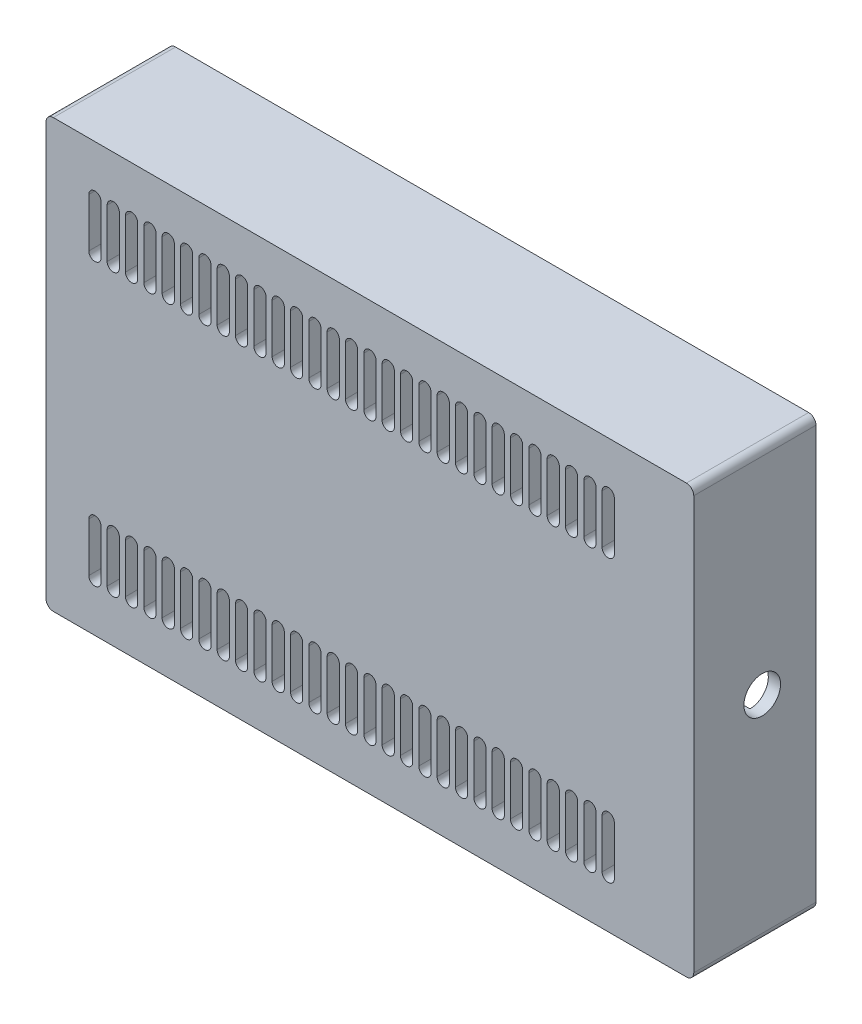
SolidWorks part; units mm, degrees
material "ABS"
ref_plane "Front Plane" through (0, 0, 0) normal (0, 0, 1) x (1, 0, 0)
ref_plane "Top Plane" through (0, 0, 0) normal (0, 1, 0) x (1, 0, 0)
ref_plane "Right Plane" through (0, 0, 0) normal (1, 0, 0) x (0, 0, -1)
sketch "Sketch1" plane through (0, 0, 0) normal (0, 0, 1) x (1, 0, 0)
  line L1 (-119.99, -87.5) -> (145.01, -87.5)
  line L2 (-119.99, -87.5) -> (-119.99, 87.5)
  line L3 (-119.99, 87.5) -> (145.01, 87.5)
  line L4 (145.01, -87.5) -> (145.01, 87.5)
  point P0 (-119.99, 0)
  dimension "D1" = 175
  dimension "D2" = 265
  dimension "D3" = 119.99
extrude "Boss-Extrude1" add sketch "Sketch1" along normal blind 50 contours L3 L4 L1 L2
shell "Shell1" thickness 5
fillet "Fillet1" radius 3 4 edges at (-119.99, -87.5, 25) (145.01, -87.5, 25) (-119.99, 87.5, 25) (145.01, 87.5, 25)
sketch "Sketch22" plane through (0, 0, 45) normal (0, 0, -1) x (-1, 0, 0)
  line L1 (-10, 35) -> (105, 35)
  line L2 (-10, 35) -> (-10, -35)
  line L3 (-10, -35) -> (105, -35)
  line L4 (105, 35) -> (105, -35)
  point P4 (105, 0)
  dimension "D1" = 70
  dimension "D2" = 115
  dimension "D3" = 10
extrude "Cut-Extrude2" cut sketch "Sketch22" against normal blind 1.5
sketch "Sketch15" plane through (0, 0, 45) normal (0, 0, -1) x (-1, 0, 0)
  circle A0 centre (-111.125, -3.89) radius 4
  circle A1 centre (-111.125, 75.49) radius 4
  circle A2 centre (111.125, -76.91) radius 4
  circle A3 centre (-111.125, -76.91) radius 4
  circle A4 centre (111.125, 75.49) radius 4
  circle A5 centre (-57.15, 75.49) radius 4
  circle A6 centre (0, 75.49) radius 4
  circle A7 centre (57.145, 75.49) radius 4
  circle A8 centre (-57.15, -76.91) radius 4
  circle A9 centre (0, -76.91) radius 4
  circle A10 centre (57.145, -76.91) radius 4
  dimension "D4" = 8
  dimension "D3" = 57.145
  dimension "D5" = 111.125
  dimension "D6" = 3.89
  dimension "D7" = 75.49
  dimension "D8" = 152.4
  dimension "D1" = 111.125
  dimension "D2" = 57.15
extrude "Boss-Extrude5" add sketch "Sketch15" along normal blind 13.95
fillet "Fillet3" radius 5 4 edges at (10, -35, 45.75) (-105, -35, 45.75) (-105, 35, 45.75) (10, 35, 45.75)
sketch "Sketch16" plane through (0, 0, 46.5) normal (0, 0, -1) x (-1, 0, 0)
  circle A0 centre (85.245, -24.97) radius 2.5
  circle A1 centre (10.115, -24.97) radius 2.5
  circle A2 centre (34.445, -9.77) radius 2.5
  circle A3 centre (3.035, 23.23) radius 2.5
  circle A4 centre (34.445, 18.13) radius 2.5
  circle A5 centre (85.665, 23.23) radius 2.5
  circle A6 centre (111.125, -76.91) radius 4 construction
  dimension "D1" = 5
  dimension "D2" = 5
  dimension "D3" = 5
  dimension "D4" = 5
  dimension "D5" = 5
  dimension "D6" = 5
  dimension "D8" = 25.88
  dimension "D7" = 51.94
  dimension "D9" = 75.13
  dimension "D10" = 51.94
  dimension "D11" = 50.8
  dimension "D12" = 15.2
  dimension "D13" = 27.9
  dimension "D14" = 48.2
  dimension "D15" = 0.42
  dimension "D16" = 82.63
extrude "Boss-Extrude6" add sketch "Sketch16" along normal blind 3
sketch "Sketch23" plane through (0, 0, 45) normal (0, 0, -1) x (-1, 0, 0)
  line L0 (-140.01, -82.5) -> (-140.01, 82.5) construction
  line L1 (-140.01, -17.5) -> (-125.01, -17.5)
  line L2 (-140.01, -17.5) -> (-140.01, 17.5)
  line L3 (-140.01, 17.5) -> (-125.01, 17.5)
  line L4 (-125.01, -17.5) -> (-125.01, 17.5)
  point P6 (-125.01, 0)
  dimension "D1" = 35
  dimension "D2" = 15
extrude "Boss-Extrude7" add sketch "Sketch23" along normal blind 23
sketch "Sketch27" plane through (0, 0, 22) normal (0, 0, -1) x (-1, 0, 0)
  line L0 (-140.01, 17.5) -> (-140.01, -17.5) construction
  circle A0 centre (-132.51, -12) radius 1.65
  circle A1 centre (-132.51, 12) radius 1.65
  dimension "D2" = 3.3
  dimension "D1" = 7.5
  dimension "D3" = 12
  dimension "D4" = 24
extrude "Cut-Extrude5" cut sketch "Sketch27" against normal up to surface (23 mm away) up to face at (-61.145, -76.91, 45)
sketch "Sketch19" plane through (0, 0, 31.05) normal (0, 0, -1) x (-1, 0, 0)
  line L0 (-57.15, 75.49) -> (-57.15, 82.5)
  line L3 (114.99, 82.5) -> (-140.01, 82.5) construction
  line L4 (-111.125, 75.49) -> (-111.125, 82.5)
  line L5 (0, 75.49) -> (0, 82.5)
  line L6 (57.145, 75.49) -> (57.145, 82.5)
  line L7 (114.99, 82.5) -> (-140.01, 82.5) construction
  line L8 (111.125, 75.49) -> (111.125, 82.5)
  circle A1 centre (0, 75.49) radius 4 construction
  circle A2 centre (57.145, 75.49) radius 4 construction
  circle A3 centre (111.125, 75.49) radius 4 construction
  circle A4 centre (-57.15, 75.49) radius 4 construction
  circle A5 centre (-111.125, 75.49) radius 4 construction
rib "Rib1" sketch "Sketch19" sketch "Sketch19" thickness 2 extrusion direction normal to sketch draft on no parameters "D1"=2
sketch "Sketch20" plane through (0, 0, 31.05) normal (0, 0, -1) x (-1, 0, 0)
  line L0 (-111.125, 75.49) -> (-140.01, 75.49)
  line L1 (-140.01, -82.5) -> (-140.01, -17.5) construction
  line L4 (-111.125, -76.91) -> (-140.01, -76.91)
  circle A0 centre (-111.125, 75.49) radius 4 construction
rib "Rib2" sketch "Sketch20" sketch "Sketch20" thickness 2 extrusion direction normal to sketch draft on no parameters "D1"=2
sketch "Sketch36" plane through (0, 0, 31.05) normal (0, 0, -1) x (-1, 0, 0)
  line L0 (-111.125, -3.89) -> (-125.01, -3.89)
  line L1 (-125.01, -17.5) -> (-125.01, 17.5) construction
rib "Rib12" sketch "Sketch36" sketch "Sketch36" thickness 2 extrusion direction normal to sketch draft on no parameters "D1"=2
mirror "Mirror1" [suppressed] about plane through (0, 0, 0) normal (1, 0, 0)
mirror "Mirror2" about plane through (0, 0, 0) normal (0, 1, 0) of "Rib1"
sketch "Sketch21" plane through (0, 0, 31.05) normal (0, 0, -1) x (-1, 0, 0)
  circle A0 centre (-111.125, 75.49) radius 1.25
  circle A1 centre (-57.15, 75.49) radius 1.25
  circle A2 centre (0, 75.49) radius 1.25
  circle A3 centre (57.145, 75.49) radius 1.25
  circle A4 centre (111.125, 75.49) radius 1.25
  circle A6 centre (111.125, -76.91) radius 1.25
  circle A7 centre (57.145, -76.91) radius 1.25
  circle A8 centre (0, -76.91) radius 1.25
  circle A9 centre (-57.15, -76.91) radius 1.25
  circle A10 centre (-111.125, -76.91) radius 1.25
  circle A11 centre (-111.125, -3.89) radius 1.25
  dimension "D1" = 2.5
extrude "Cut-Extrude1" cut sketch "Sketch21" against normal up to surface (13.95 mm away) up to face at (-47.5, 0, 45)
fillet "Fillet2" [suppressed] radius 0.6
sketch "Sketch25" plane through (125.01, 0, 0) normal (-1, 0, 0) x (0, 0, 1)
  line L0 (22, -17.5) -> (22, 17.5) construction
  circle A0 centre (22, 0) radius 7.5
  dimension "D1" = 15
extrude "Cut-Extrude3" cut sketch "Sketch25" against normal blind 21.1
fillet "Fillet4" radius 3 2 edges at (125.01, 17.5, 33.5) (125.01, -17.5, 33.5)
sketch "Sketch28" plane through (0, 0, 50) normal (0, 0, 1) x (1, 0, 0)
  line L0 (-119.99, -84.5) -> (-119.99, 84.5) construction
  line L1 (-116.99, 87.5) -> (142.01, 87.5) construction
  line L2 (-102.49, 47.5) -> (-102.49, 67.5)
  line L3 (-97.49, 47.5) -> (-97.49, 67.5)
  arc A0 (-97.49, 67.5) -> (-102.49, 67.5) centre (-99.99, 67.5) ccw
  arc A1 (-102.49, 47.5) -> (-97.49, 47.5) centre (-99.99, 47.5) ccw
  dimension "D1" = 5
  dimension "D2" = 20
  dimension "D3" = 20
  dimension "D5" = 20
extrude "Cut-Extrude4" cut sketch "Sketch28" against normal blind 15
pattern_linear "LPattern2" count 29 spacing 7.5 along (1, 0, 0) of "Cut-Extrude4"
mirror "Mirror3" about plane through (0, 0, 0) normal (0, 1, 0) of "LPattern2", "Cut-Extrude4"
sketch "Sketch33" plane through (-119.99, 0, 0) normal (-1, 0, 0) x (0, 0, 1)
  line L1 (44.95, -5.3) -> (32.95, -5.3)
  line L2 (44.95, -5.3) -> (44.95, -18.8)
  line L3 (44.95, -18.8) -> (32.95, -18.8)
  line L4 (32.95, -5.3) -> (32.95, -18.8)
  point P4 (32.95, -12.05)
  point P6 (38.95, -5.3)
  dimension "D1" = 12.05
  dimension "D2" = 13.5
  dimension "D3" = 12
  dimension "D4" = 38.95
extrude "Cut-Extrude6" cut sketch "Sketch33" against normal blind 10.5
sketch "Sketch37" plane through (0, 0, 0) normal (0, 0, -1) x (-1, 0, 0)
  line L0 (119.99, -84.5) -> (119.99, 84.5) construction
  line L1 (117.49, -85) -> (-142.51, -85) construction
  line L2 (117.49, -85) -> (117.49, 85) construction
  line L3 (117.49, 85) -> (-142.51, 85) construction
  line L4 (-142.51, -85) -> (-142.51, 85) construction
  line L5 (116.99, -87.5) -> (-142.01, -87.5) construction
  line L6 (-145.01, -84.5) -> (-145.01, 84.5) construction
  line L7 (116.99, 87.5) -> (-142.01, 87.5) construction
  dimension "D1" = 2.5
  dimension "D2" = 2.5
  dimension "D3" = 2.5
  dimension "D4" = 2.5
